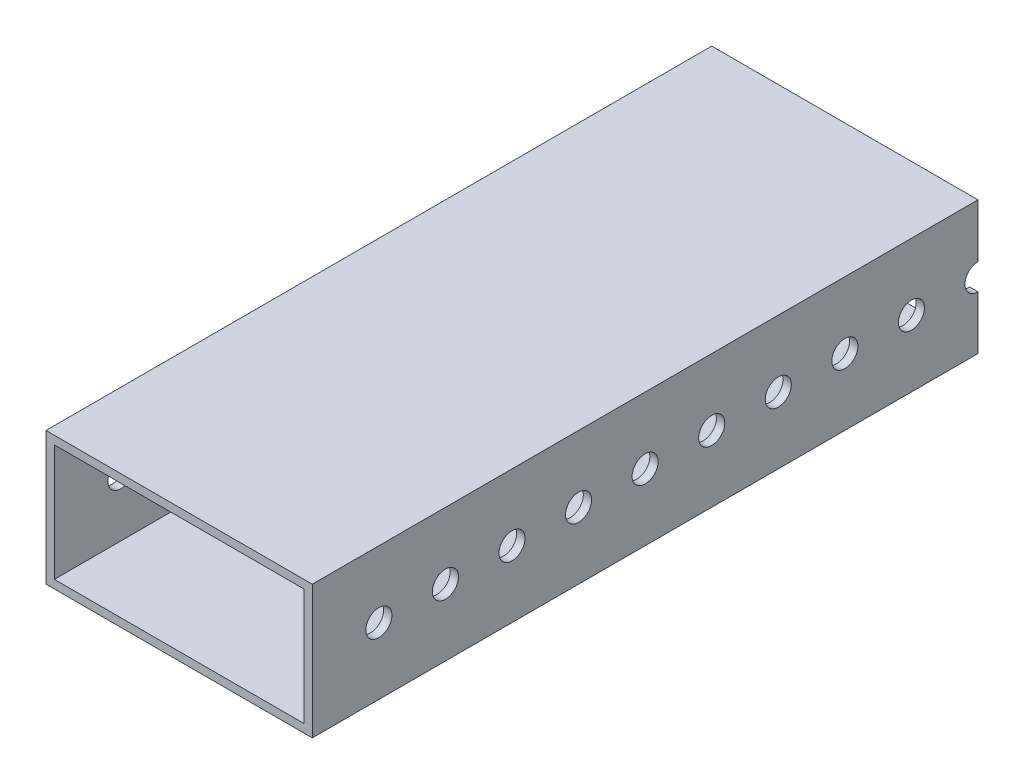
SolidWorks part; units mm, degrees
material "6061 Alloy"
ref_plane "Front Plane" through (0, 0, 0) normal (0, 0, 1) x (1, 0, 0)
ref_plane "Top Plane" through (0, 0, 0) normal (0, 1, 0) x (1, 0, 0)
ref_plane "Right Plane" through (0, 0, 0) normal (1, 0, 0) x (0, 0, -1)
sketch "Sketch1" plane through (0, 0, 0) normal (0, 0, 1) x (1, 0, 0)
  line L0 (1.5875, 1.5875) -> (49.2125, 1.5875)
  line L1 (0, 0) -> (50.8, 0)
  line L2 (0, 0) -> (0, 25.4)
  line L3 (0, 25.4) -> (50.8, 25.4)
  line L4 (50.8, 0) -> (50.8, 25.4)
  line L5 (49.2125, 1.5875) -> (49.2125, 23.8125)
  line L6 (1.5875, 23.8125) -> (49.2125, 23.8125)
  line L7 (1.5875, 1.5875) -> (1.5875, 23.8125)
  dimension "D1" = 50.8
  dimension "D2" = 25.4
  dimension "D3" = 1.5875
extrude "Boss-Extrude1" add sketch "Sketch1" along normal blind 127
sketch "Sketch2" plane through (50.8, 0, 0) normal (1, 0, 0) x (0, 0, -1)
  line L0 (-127, 0) -> (-127, 25.4) construction
  line L1 (-114.3, 12.7) -> (-101.6, 12.7) construction
  circle A0 centre (-114.3, 12.7) radius 2.4892
  circle A1 centre (-101.6, 12.7) radius 2.4892
  circle A2 centre (-88.9, 12.7) radius 2.4892
  circle A3 centre (-76.2, 12.7) radius 2.4892
  circle A4 centre (-63.5, 12.7) radius 2.4892
  circle A5 centre (-50.8, 12.7) radius 2.4892
  circle A6 centre (-38.1, 12.7) radius 2.4892
  circle A7 centre (-25.4, 12.7) radius 2.4892
  circle A8 centre (-12.7, 12.7) radius 2.4892
  circle A9 centre (0, 12.7) radius 2.4892
  circle A10 centre (12.7, 12.7) radius 2.4892
  point P5 (-127, 12.7)
  dimension "D1" = 4.9784
  dimension "D2" = 12.7
  dimension "D4" = 12.7
  dimension "D3" = 11
extrude "Cut-Extrude1" cut sketch "Sketch2" against normal through all
